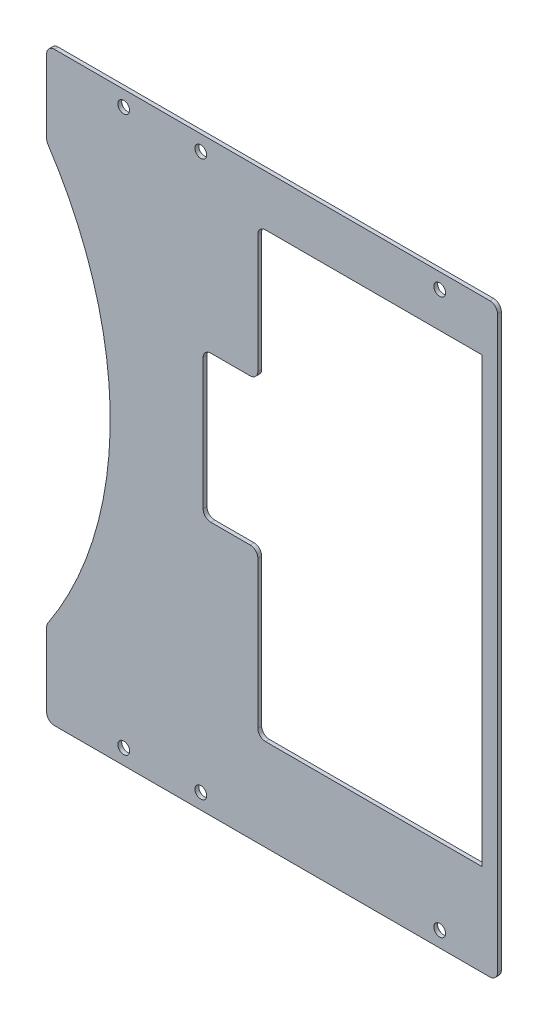
SolidWorks part; units mm, degrees
material "Thornel Mat VMA"
ref_plane "前视基准面" through (0, 0, 0) normal (0, 0, 1) x (1, 0, 0)
ref_plane "上视基准面" through (0, 0, 0) normal (0, 1, 0) x (1, 0, 0)
ref_plane "右视基准面" through (0, 0, 0) normal (1, 0, 0) x (0, 0, -1)
other "Configuration Table"
sketch "草图1" plane through (0, 0, 0) normal (0, 0, 1) x (1, 0, 0)
  line L0 (0, 72) -> (0, -72) construction
  line L1 (0, 0) -> (50000, 0) construction
  line L2 (0, 72) -> (20, 72) construction
  line L3 (82, -72) -> (20, -72) construction
  line L4 (82, -72) -> (82, 72) construction
  line L5 (82, 72) -> (20, 72) construction
  line L6 (20, -72) -> (20, 72) construction
  line L7 (82, -72) -> (20, 72) construction
  line L8 (82, 72) -> (20, -72) construction
  line L10 (97, -76) -> (-20, -76)
  line L11 (97, -76) -> (97, 76)
  line L12 (97, 76) -> (-20, 76)
  line L13 (-20, -76) -> (-20, 76)
  line L14 (97, -76) -> (-20, 76) construction
  line L15 (97, 76) -> (-20, -76) construction
  circle A0 centre (0, 72) radius 1.525
  circle A1 centre (0, -72) radius 1.525
  circle A2 centre (20, 72) radius 1.525
  circle A3 centre (82, 72) radius 1.525
  circle A4 centre (82, -72) radius 1.525
  circle A5 centre (20, -72) radius 1.525
  point P4 (0, 0)
  point P9 (51, 0)
  point P18 (38.5, 0)
  dimension "D4" = 3.05
  dimension "D1" = 144
  dimension "D2" = 62
  dimension "D3" = 20
  dimension "D5" = 4
  dimension "D6" = 20
  dimension "D7" = 15
extrude "凸台-拉伸1" add sketch "草图1" along normal blind 1
sketch "草图2" plane through (0, 0, 0) normal (0, 0, -1) x (-1, 0, 0)
  line L1 (-97, 62.8) -> (-34.798, 62.8)
  line L2 (-97, 62.8) -> (-97, -52.2)
  line L3 (-97, -52.2) -> (-34.798, -52.2)
  line L4 (-34.798, 62.8) -> (-34.798, -52.2)
  line L5 (-97, 62.8) -> (-34.798, -52.2) construction
  line L6 (-97, -52.2) -> (-34.798, 62.8) construction
  line L7 (-97, -76) -> (-97, 76) construction
  line L8 (-44.7368, 5.3) -> (-50044.7368, 5.3) construction
  line L9 (-44.7368, -39.2153) -> (-44.7368, 49.8153) construction
  line L10 (-48.2421, -42.5084) -> (-83.5559, -42.5084) construction
  line L11 (-83.5559, -42.5084) -> (-48.2421, -42.5084) construction
  line L12 (-65.899, -42.5084) -> (-65.899, 49957.4916) construction
  circle A0 centre (101, 0) radius 97.5
  arc A1 (39.8524, -75.9422) -> (162.1476, -75.9422) centre (101, 0) ccw construction
  spline S0 degree 1 poles (-48.2421, -42.5084) (-48.2433, -40.7842) knots 0 0 1 1 construction
  point P5 (-65.899, 5.3)
  point P21 (-44.7368, 5.3)
  point P31 (-65.899, -42.5084)
  dimension "D1" = 115
extrude "切除-拉伸1" cut sketch "草图2" against normal blind 10
sketch "草图3" plane through (0, 0, 0) normal (0, 0, -1) x (-1, 0, 0)
  line L0 (-40.6, 28) -> (-40.6, -10) construction
  line L1 (-40.6, 9) -> (49959.4, 9) construction
  line L3 (-40.6, 28) -> (-20.6, 28)
  line L4 (-40.6, 28) -> (-40.6, -10)
  line L5 (-40.6, -10) -> (-20.6, -10)
  line L6 (-20.6, 28) -> (-20.6, -10)
  point P6 (-40.6, 9)
  dimension "D1" = 20
extrude "切除-拉伸2" cut sketch "草图3" against normal blind 10
fillet "圆角1" radius 2 12 edges at (20.6, 28, 0.5) (20.6, -10, 0.5) (34.798, -10, 0.5) (34.798, -52.2, 0.5) (97, -76, 0.5) (-20, -76, 0.5) (-20, 54.2702, 0.5) (-20, -54.2702, 0.5) (-20, 76, 0.5) (34.798, 62.8, 0.5) (34.798, 28, 0.5) (97, 76, 0.5)
sketch "草图6" plane through (0, 0, 1) normal (0, 0, 1) x (1, 0, 0)
  line L0 (97, 62.8) -> (36.798, 62.8) construction
  line L1 (93, 62.8) -> (97, 62.8)
  line L2 (93, 62.8) -> (93, -52.2)
  line L3 (93, -52.2) -> (97, -52.2)
  line L4 (97, 62.8) -> (97, -52.2)
  line L5 (36.798, -52.2) -> (97, -52.2) construction
  line L6 (97, -74) -> (97, -52.2) construction
  point P6 (89.1316, -52.2)
  point P11 (97, 62.8)
  dimension "D1" = 4
extrude "凸台-拉伸2" add sketch "草图6" against normal up to surface (1 mm away) up to face at (30.8702, 3.9923, 0)
